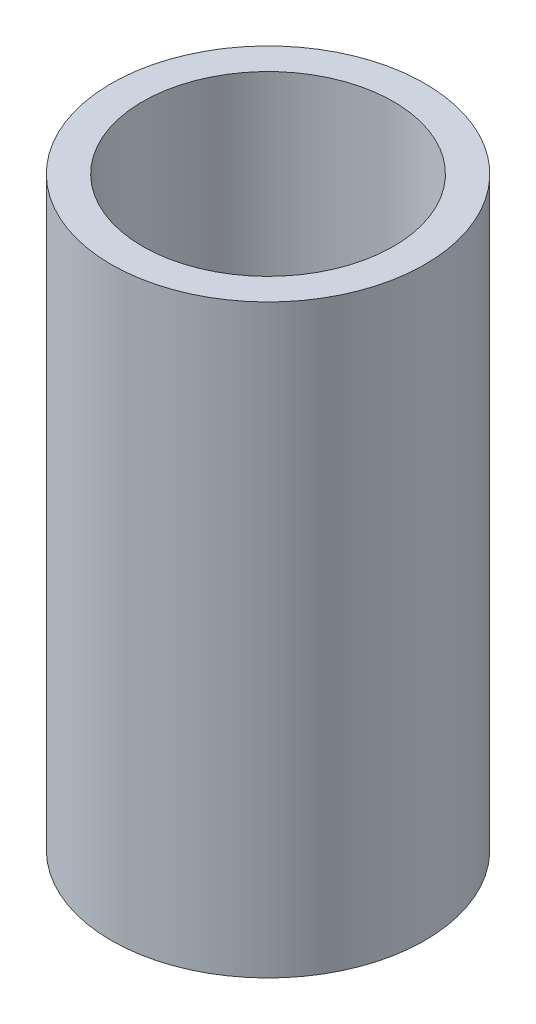
SolidWorks part; units mm, degrees
ref_plane "Front Plane" through (0, 0, 0) normal (0, 0, 1) x (1, 0, 0)
ref_plane "Top Plane" through (0, 0, 0) normal (0, 1, 0) x (1, 0, 0)
ref_plane "Right Plane" through (0, 0, 0) normal (1, 0, 0) x (0, 0, -1)
sketch "Sketch1" plane through (0, 0, 0) normal (0, 1, 0) x (1, 0, 0)
  circle A0 centre (0, 0) radius 7.5
  circle A1 centre (0, 0) radius 6
  dimension "D1" = 15
  dimension "D2" = 12
extrude "Boss-Extrude1" add sketch "Sketch1" along normal mid plane 28
